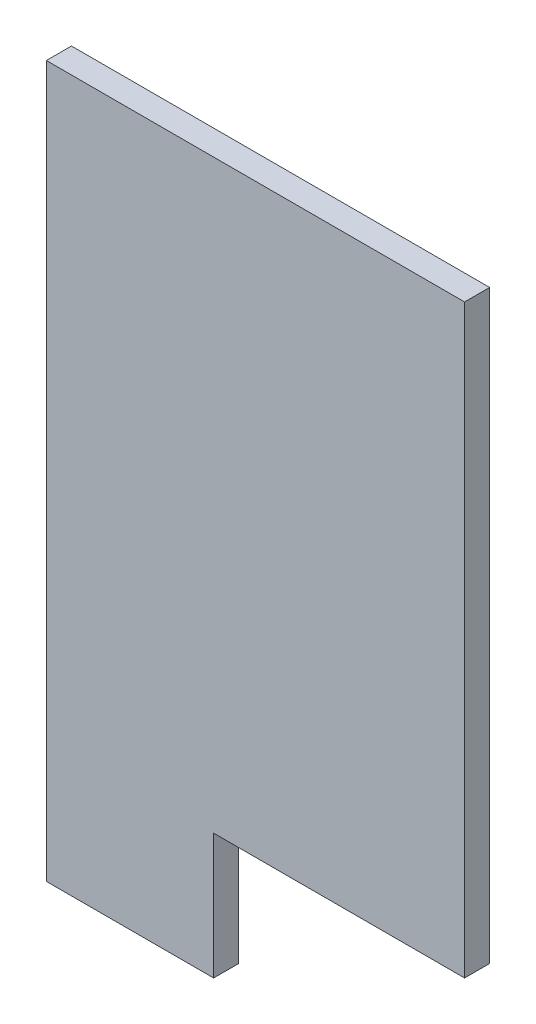
SolidWorks part; units mm, degrees
ref_plane "前视基准面" through (0, 0, 0) normal (0, 0, 1) x (1, 0, 0)
ref_plane "上视基准面" through (0, 0, 0) normal (0, 1, 0) x (1, 0, 0)
ref_plane "右视基准面" through (0, 0, 0) normal (1, 0, 0) x (0, 0, -1)
sketch "草图1" plane through (0, 0, 0) normal (0, 0, 1) x (1, 0, 0)
  line L1 (-25, 35) -> (25, 35)
  line L2 (-25, 35) -> (-25, -35)
  line L3 (-5, -35) -> (25, -35)
  line L4 (25, 35) -> (25, -35)
  line L5 (-25, 35) -> (25, -35) construction
  line L6 (-25, -35) -> (25, 35) construction
  line L8 (-25, -35) -> (-25, -50)
  line L9 (-25, -50) -> (-5, -50)
  line L10 (-5, -35) -> (-5, -50)
  point P0 (0, 0)
  dimension "D1" = 70
  dimension "D2" = 50
  dimension "D3" = 15
  dimension "D4" = 20
extrude "凸台-拉伸1" add sketch "草图1" along normal blind 3
